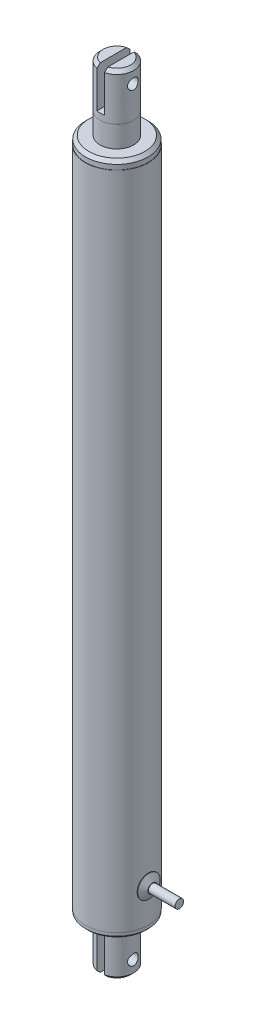
SolidWorks part; units mm, degrees
ref_plane "Front Plane" through (0, 0, 0) normal (0, 0, 1) x (1, 0, 0)
ref_plane "Top Plane" through (0, 0, 0) normal (0, 1, 0) x (1, 0, 0)
ref_plane "Right Plane" through (0, 0, 0) normal (1, 0, 0) x (0, 0, -1)
sketch "Sketch1" plane through (0, 0, 0) normal (0, 1, 0) x (1, 0, 0)
  circle A0 centre (0, 0) radius 14.986
  dimension "D1" = 29.972
extrude "Boss-Extrude1" add sketch "Sketch1" along normal blind 313.944
sketch "Sketch2" plane through (0, 0, 0) normal (0, -1, 0) x (1, 0, 0)
  circle A0 centre (0, 0) radius 14.859
  dimension "D1" = 29.718
extrude "Boss-Extrude2" add sketch "Sketch2" along normal blind 2.54
chamfer "Chamfer1" distance 1.016 angle 45 1 edges at (0, -2.54, -14.859)
sketch "Sketch3" plane through (0, -2.54, 0) normal (0, -1, 0) x (1, 0, 0)
  circle A0 centre (0, 0) radius 8.001
  dimension "D1" = 16.002
extrude "Boss-Extrude3" add sketch "Sketch3" along normal blind 22.098
chamfer "Chamfer2" distance 1.524 angle 45 1 edges at (0, -24.638, -8.001)
ref_plane "Plane1" through (-8.001, 0, 0) normal (-1, 0, 0) x (0, 0, 1)
sketch "Sketch4" plane through (-8.001, 0, 0) normal (-1, 0, 0) x (0, 0, 1)
  line L0 (-6.477, -24.638) -> (6.477, -24.638) construction
  circle A0 centre (0, -17.638) radius 2.54
  dimension "D1" = 5.08
  dimension "D2" = 7
extrude "Cut-Extrude1" cut sketch "Sketch4" against normal blind 21.59
ref_plane "Plane2" through (0, 0, -8.001) normal (0, 0, -1) x (-1, 0, 0)
sketch "Sketch5" plane through (0, 0, -8.001) normal (0, 0, -1) x (-1, 0, 0)
  line L0 (-8.001, -20.178) -> (-8.001, -23.114) construction
  line L1 (1.651, -28.9772) -> (-1.905, -28.9772)
  line L2 (1.651, -28.9772) -> (1.651, -6.096)
  line L3 (1.651, -6.096) -> (-1.905, -6.096)
  line L4 (-1.905, -28.9772) -> (-1.905, -6.096)
  line L7 (-6.477, -24.638) -> (6.477, -24.638) construction
  dimension "D1" = 3.556
  dimension "D2" = 6.096
  dimension "D3" = 18.542
extrude "Cut-Extrude2" cut sketch "Sketch5" against normal blind 21.59
ref_plane "Plane3" through (14.986, 0, 0) normal (1, 0, 0) x (0, 0, -1)
sketch "Sketch6" plane through (14.986, 0, 0) normal (1, 0, 0) x (0, 0, -1)
  circle A0 centre (0, 16.2013) radius 5.334
  dimension "D1" = 10.668
extrude "Boss-Extrude4" add sketch "Sketch6" along normal blind 2.032 separate body contours A0
chamfer "Chamfer3" distance 1.778 angle 60 1 edges at (17.018, 16.2013, -5.334)
sketch "Sketch7" plane through (17.018, 0, 0) normal (1, 0, 0) x (0, 0, -1)
  circle A0 centre (0, 16.2013) radius 2.032
  dimension "D1" = 4.064
extrude "Boss-Extrude5" add sketch "Sketch7" along normal blind 12.7 contours A0
sketch "Sketch8" plane through (0, 313.944, 0) normal (0, 1, 0) x (1, 0, 0)
  circle A0 centre (0, 0) radius 14.859
  dimension "D1" = 29.718
extrude "Boss-Extrude6" add sketch "Sketch8" along normal blind 3.81
chamfer "Chamfer4" distance 1.524 angle 45 1 edges at (0, 317.754, 14.859)
sketch "Sketch9" plane through (0, 317.754, 0) normal (0, 1, 0) x (1, 0, 0)
  circle A0 centre (0, 0) radius 8.001
  dimension "D1" = 16.002
extrude "Boss-Extrude7" add sketch "Sketch9" along normal blind 10.16
sketch "Sketch10" plane through (0, 327.914, 0) normal (0, 1, 0) x (1, 0, 0)
  circle A0 centre (0, 0) radius 8.001
extrude "Boss-Extrude8" add sketch "Sketch10" along normal blind 22 separate body
chamfer "Chamfer5" distance 1.524 angle 45 1 edges at (0, 349.914, 8.001)
ref_plane "Plane4" through (-8.001, 0, 0) normal (-1, 0, 0) x (0, 0, 1)
sketch "Sketch11" plane through (-8.001, 0, 0) normal (-1, 0, 0) x (0, 0, 1)
  line L0 (6.477, 349.914) -> (-6.477, 349.914) construction
  circle A0 centre (0, 342.914) radius 2.54
  dimension "D1" = 5.08
  dimension "D2" = 7
extrude "Cut-Extrude3" cut sketch "Sketch11" against normal blind 21.844
ref_plane "Plane5" through (0, 0, -8.001) normal (0, 0, -1) x (-1, 0, 0)
sketch "Sketch12" plane through (0, 0, -8.001) normal (0, 0, -1) x (-1, 0, 0)
  line L0 (-8.001, 340.374) -> (-8.001, 327.914) construction
  line L1 (-1.905, 330.864) -> (1.651, 330.864)
  line L2 (-1.905, 330.864) -> (-1.905, 349.914)
  line L3 (-1.905, 349.914) -> (1.651, 349.914)
  line L4 (1.651, 330.864) -> (1.651, 349.914)
  line L5 (6.477, 349.914) -> (-6.477, 349.914) construction
  point P8 (-0.127, 330.864)
  dimension "D1" = 6.096
  dimension "D2" = 3.556
  dimension "D3" = 0
  dimension "D4" = 19.05
extrude "Cut-Extrude4" cut sketch "Sketch12" against normal blind 21.844 contours L4 L3 L2 L1
equation "\"stroke\"= 6"
equation "\"D1@Boss-Extrude1\"= \"stroke\" + 6.36"
